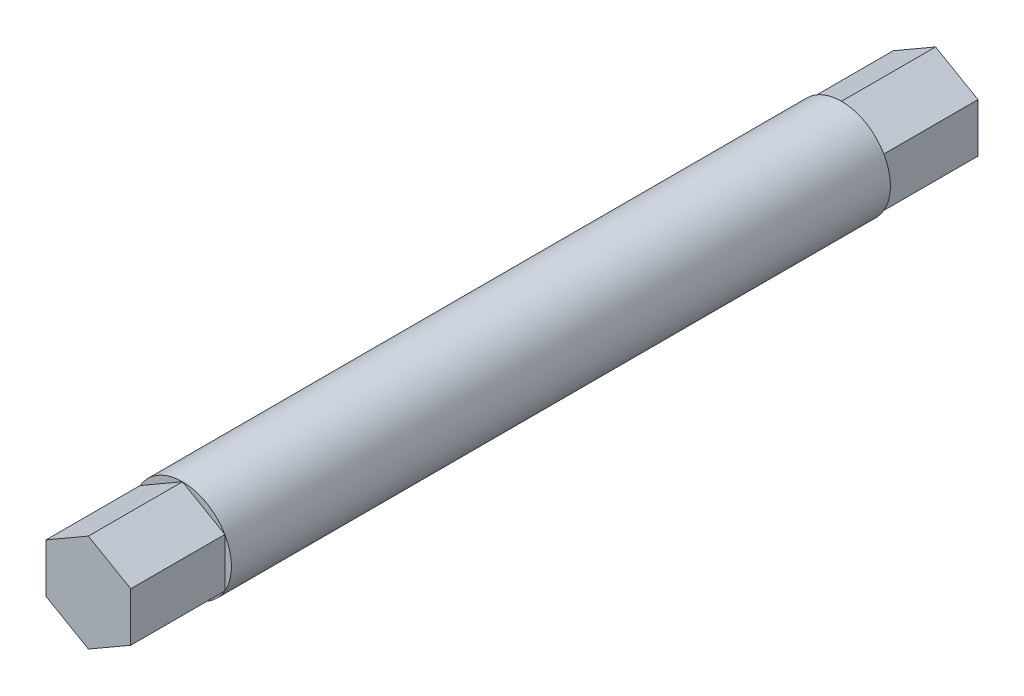
SolidWorks part; units mm, degrees
ref_plane "Alzado" through (0, 0, 0) normal (0, 0, 1) x (1, 0, 0)
ref_plane "Planta" through (0, 0, 0) normal (0, 1, 0) x (1, 0, 0)
ref_plane "Vista lateral" through (0, 0, 0) normal (1, 0, 0) x (0, 0, -1)
sketch "Croquis1" plane through (0, 0, 0) normal (0, 0, 1) x (1, 0, 0)
  line L1 (0, 5.1962) -> (-4.5, 2.5981)
  line L2 (-4.5, 2.5981) -> (-4.5, -2.5981)
  line L3 (-4.5, -2.5981) -> (0, -5.1962)
  line L4 (0, -5.1962) -> (4.5, -2.5981)
  line L5 (4.5, -2.5981) -> (4.5, 2.5981)
  line L6 (4.5, 2.5981) -> (0, 5.1962)
  circle A0 centre (0, 0) radius 4.5 construction
  dimension "D1" = 9
extrude "Saliente-Extruir1" add sketch "Croquis1" along normal blind 10
sketch "Croquis2" plane through (0, 0, 10) normal (0, 0, 1) x (1, 0, 0)
  circle A0 centre (0, 0) radius 5.1962
extrude "Saliente-Extruir3" add sketch "Croquis2" along normal blind 70
sketch "Croquis3" plane through (0, 0, 80) normal (0, 0, 1) x (1, 0, 0)
  line L1 (0, 5.1962) -> (-4.5, 2.5981)
  line L2 (-4.5, 2.5981) -> (-4.5, -2.5981)
  line L3 (-4.5, -2.5981) -> (0, -5.1962)
  line L4 (0, -5.1962) -> (4.5, -2.5981)
  line L5 (4.5, -2.5981) -> (4.5, 2.5981)
  line L6 (4.5, 2.5981) -> (0, 5.1962)
  circle A0 centre (0, 0) radius 4.5 construction
extrude "Saliente-Extruir4" add sketch "Croquis3" along normal blind 10
